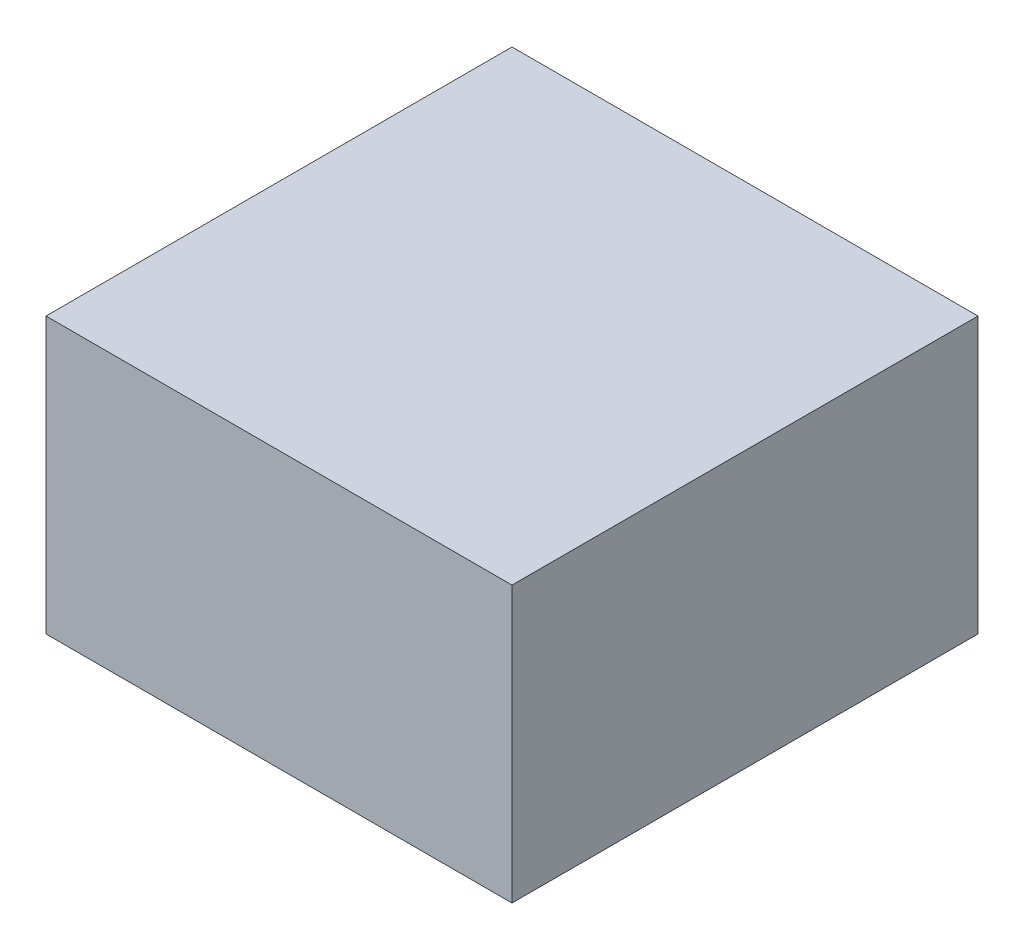
SolidWorks part; units mm, degrees
ref_plane "Front Plane" through (0, 0, 0) normal (0, 0, 1) x (1, 0, 0)
ref_plane "Top Plane" through (0, 0, 0) normal (0, 1, 0) x (1, 0, 0)
ref_plane "Right Plane" through (0, 0, 0) normal (1, 0, 0) x (0, 0, -1)
sketch "Sketch1" plane through (0, 0, 0) normal (0, 1, 0) x (1, 0, 0)
  line L1 (55, -55) -> (-55, -55)
  line L2 (55, -55) -> (55, 55)
  line L3 (55, 55) -> (-55, 55)
  line L4 (-55, -55) -> (-55, 55)
  line L5 (55, -55) -> (-55, 55) construction
  line L6 (55, 55) -> (-55, -55) construction
  point P0 (0, 0)
  dimension "D1" = 110
  dimension "D2" = 110
extrude "Boss-Extrude1" add sketch "Sketch1" along normal blind 65
